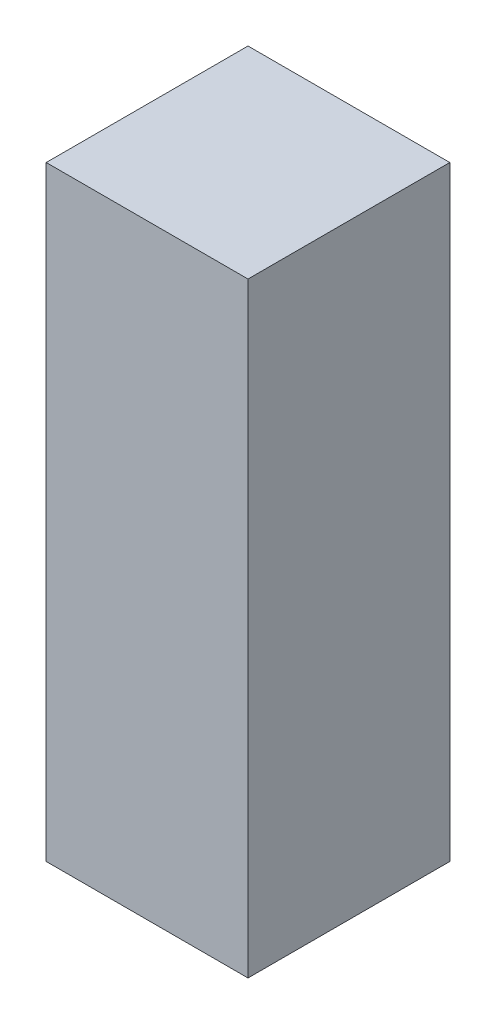
SolidWorks part; units mm, degrees
ref_plane "Front Plane" through (0, 0, 0) normal (0, 0, 1) x (1, 0, 0)
ref_plane "Top Plane" through (0, 0, 0) normal (0, 1, 0) x (1, 0, 0)
ref_plane "Right Plane" through (0, 0, 0) normal (1, 0, 0) x (0, 0, -1)
sketch "Sketch1" plane through (0, 0, 0) normal (0, 1, 0) x (1, 0, 0)
  line L1 (-5000, 5000) -> (5000, 5000)
  line L2 (-5000, 5000) -> (-5000, -5000)
  line L3 (-5000, -5000) -> (5000, -5000)
  line L4 (5000, 5000) -> (5000, -5000)
  dimension "D1" = 10000
  dimension "D2" = 10000
  dimension "D3" = 5000
  dimension "D4" = 5000
extrude "Boss-Extrude1" add sketch "Sketch1" along normal blind 30000
